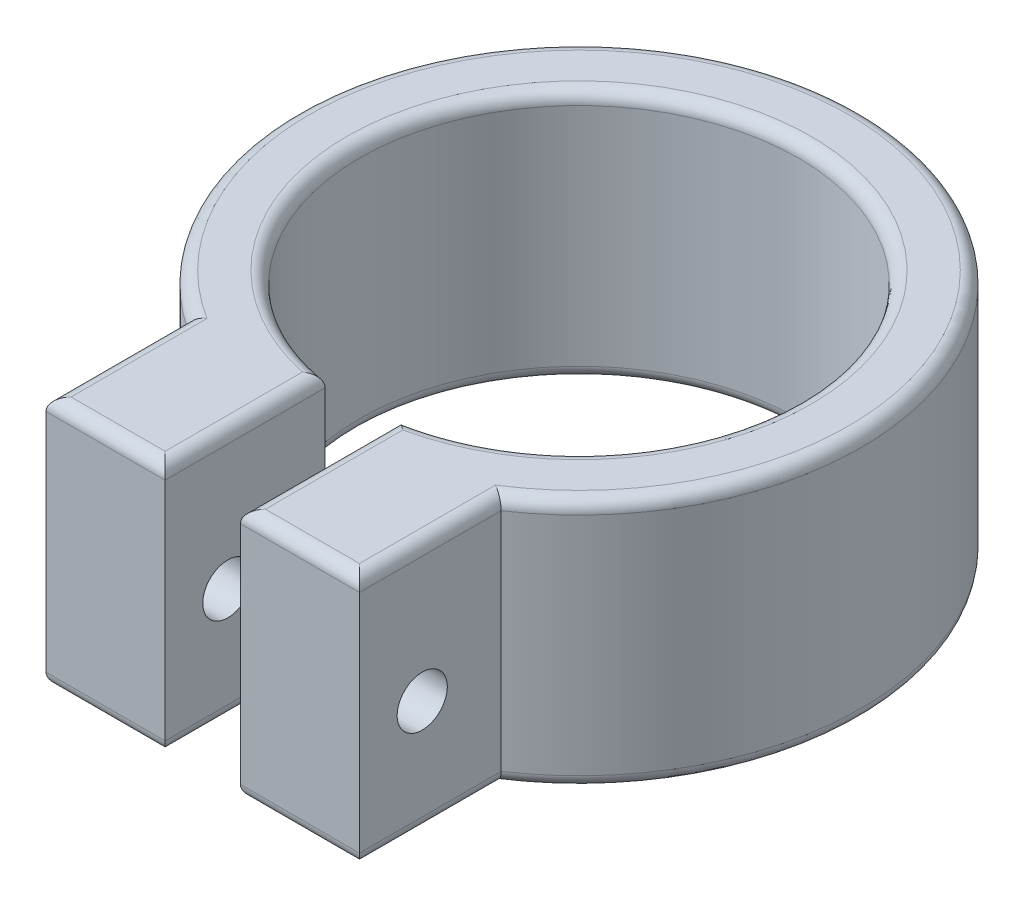
SolidWorks part; units mm, degrees
ref_plane "Front Plane" through (0, 0, 0) normal (0, 0, 1) x (1, 0, 0)
ref_plane "Top Plane" through (0, 0, 0) normal (0, 1, 0) x (1, 0, 0)
ref_plane "Right Plane" through (0, 0, 0) normal (1, 0, 0) x (0, 0, -1)
sketch "Sketch1" plane through (0, 0, 0) normal (0, 1, 0) x (1, 0, 0)
  line L0 (0, 30) -> (0, 0)
  line L1 (0, 0) -> (45, 0)
  line L2 (45, 0) -> (45, 30)
  arc A0 (45, 30) -> (0, 30) centre (22.5, 30) ccw
  circle A1 centre (22.5, 30) radius 17.5
  dimension "D1" = 30
  dimension "D4" = 35
  dimension "D2" = 30
  dimension "D3" = 45
extrude "Boss-Extrude1" add sketch "Sketch1" along normal blind 20
sketch "Sketch2" plane through (0, 20, 0) normal (0, 1, 0) x (1, 0, 0)
  line L0 (0, 0) -> (45, 0) construction
  line L1 (19.5, 0) -> (25.5, 0)
  line L2 (19.5, 0) -> (19.5, 12.7591)
  line L3 (19.5, 12.7591) -> (25.5, 12.7591)
  line L4 (25.5, 0) -> (25.5, 12.7591)
  circle A0 centre (22.5, 30) radius 17.5 construction
  dimension "D1" = 6
  dimension "D2" = 19.5
extrude "Cut-Extrude2" cut sketch "Sketch2" against normal blind 20
sketch "Sketch5" plane through (0, 20, 0) normal (0, 1, 0) x (1, 0, 0)
  line L0 (45, 30) -> (45, 0)
  line L1 (45, 0) -> (35, 0)
  line L2 (25.5, 0) -> (45, 0) construction
  line L3 (35, 0) -> (35, 11.2917)
  line L4 (0, 30) -> (0, 0)
  line L5 (0, 0) -> (10, 0)
  line L6 (0, 0) -> (19.5, 0) construction
  line L7 (10, 0) -> (10, 11.2917)
  arc A0 (45, 30) -> (0, 30) centre (22.5, 30) ccw construction
  arc A1 (45, 30) -> (0, 30) centre (22.5, 30) cw
  dimension "D1" = 10
  dimension "D2" = 10
extrude "Cut-Extrude5" cut sketch "Sketch5" against normal blind 20 contours L7 A1 L6 | L4 A1 L3
fillet "Fillet5" radius 1 16 edges at (35, 0, -5.6459) (35, 20, -5.6459) (10, 0, -5.6459) (10, 20, -5.6459) (14.75, 0, 0) (14.75, 20, 0) (22.5, 0, -47.5) (22.5, 20, -47.5) (25.5, 20, -6.3795) (25.5, 0, -6.3795) (19.5, 0, -6.3795) (19.5, 20, -6.3795) (22.5, 0, -52.5) (30.25, 0, 0) (30.25, 20, 0) (22.5, 20, -52.5)
sketch "Sketch6" plane through (35, 0, 0) normal (1, 0, 0) x (0, 0, -1)
  circle A0 centre (5, 9) radius 2
  dimension "D2" = 4
  dimension "D1" = 10
  dimension "D3" = 5
extrude "Cut-Extrude7" cut sketch "Sketch6" against normal blind 29
cosmetic thread "Cosmetic Thread1" parameters "D1"=4, "D2"=5
cosmetic thread "Cosmetic Thread2" parameters "D1"=4, "D2"=5
